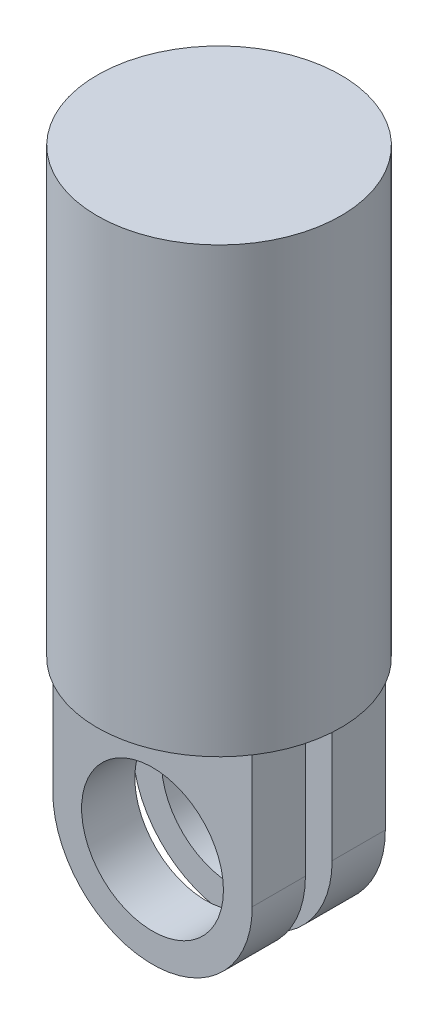
SolidWorks part; units mm, degrees
ref_plane "Front Plane" through (0, 0, 0) normal (0, 0, 1) x (1, 0, 0)
ref_plane "Top Plane" through (0, 0, 0) normal (0, 1, 0) x (1, 0, 0)
ref_plane "Right Plane" through (0, 0, 0) normal (1, 0, 0) x (0, 0, -1)
sketch "Sketch1" plane through (0, 0, 0) normal (0, 1, 0) x (1, 0, 0)
  circle A0 centre (0, 0) radius 27.5
  dimension "D1" = 55
extrude "Boss-Extrude1" add sketch "Sketch1" along normal blind 100
ref_plane "Plane1" through (0, 0, 10.011) normal (0, 0, 1) x (1, 0, 0)
sketch "Sketch6" plane through (0, 0, 10.011) normal (0, 0, 1) x (1, 0, 0)
  line L0 (0, 0) -> (0, -30.0089) construction
  line L1 (-27.5, 0) -> (27.5, 0) construction
  line L2 (22.5, 0) -> (-22.5, 0)
  line L3 (22.5, 0) -> (22.5, -30)
  line L5 (-22.5, 0) -> (-22.5, -30)
  line L6 (22.5, 0) -> (-22.5, -30) construction
  line L7 (22.5, -30) -> (-22.5, 0) construction
  arc A1 (-22.5, -30) -> (22.5, -30) centre (0, -30.0089) ccw
  circle A2 centre (0, -30.0089) radius 16
  point P3 (0, -15)
  dimension "D4" = 32
  dimension "D2" = 45
  dimension "D1" = 30
  dimension "D5" = 30.0089
extrude "Boss-Extrude3" add sketch "Sketch6" against normal blind 7 and the other way blind 5
mirror "Mirror1" about plane through (0, 0, 0) normal (0, 0, 1) of "Boss-Extrude3"
